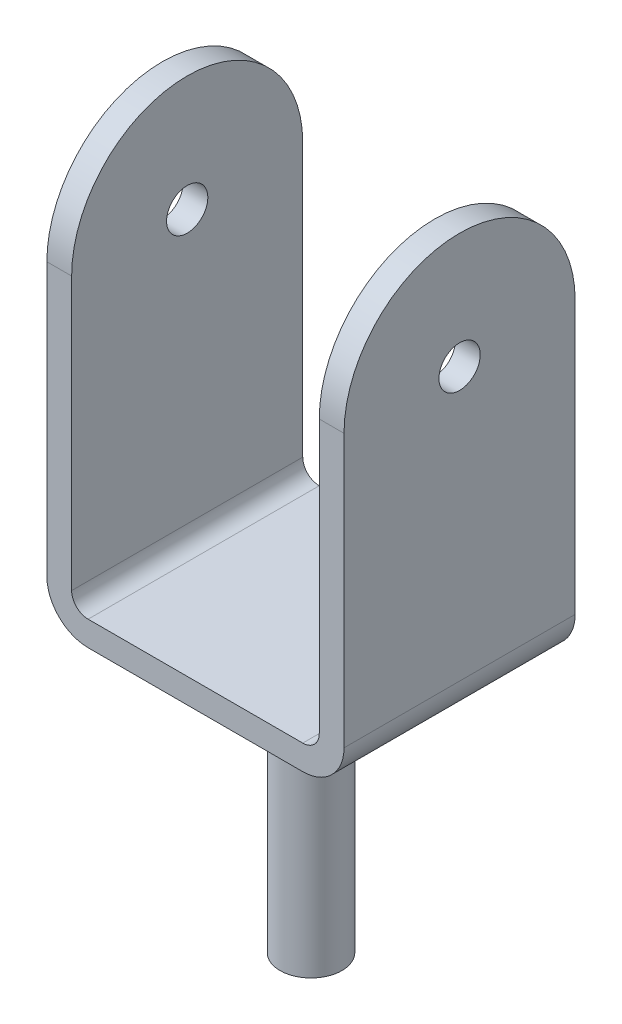
SolidWorks part; units mm, degrees
ref_plane "Front Plane" through (0, 0, 0) normal (0, 0, 1) x (1, 0, 0)
ref_plane "Top Plane" through (0, 0, 0) normal (0, 1, 0) x (1, 0, 0)
ref_plane "Right Plane" through (0, 0, 0) normal (1, 0, 0) x (0, 0, -1)
sketch "Sketch1" plane through (0, 0, 0) normal (0, 1, 0) x (1, 0, 0)
  circle A0 centre (0, 0) radius 37.5
  dimension "D1" = 75
extrude "Boss-Extrude1" add sketch "Sketch1" along normal blind 325 contours A0
sketch "Sketch2" plane through (0, 325, 0) normal (0, 1, 0) x (1, 0, 0)
  line L1 (-180, -140) -> (180, -140)
  line L2 (-180, -140) -> (-180, 140)
  line L3 (-180, 140) -> (180, 140)
  line L4 (180, -140) -> (180, 140)
  line L5 (0, 140) -> (0, -140) construction
  line L6 (-180, 0) -> (180, 0) construction
  point P0 (0, 0)
  dimension "D1" = 280
  dimension "D2" = 360
extrude "Boss-Extrude2" add sketch "Sketch2" along normal blind 520
sketch "Sketch3" plane through (0, 0, 140) normal (0, 0, 1) x (1, 0, 0)
  line L0 (-150, 845) -> (150, 845)
  line L1 (-180, 845) -> (180, 845) construction
  line L2 (-150, 845) -> (-150, 355)
  line L6 (-150, 355) -> (150, 355)
  line L7 (-180, 325) -> (180, 325) construction
  line L8 (-180, 325) -> (180, 325)
  line L9 (150, 845) -> (150, 355)
  line M5 (180, 845) -> (-180, 845)
  dimension "D2" = 30
  dimension "D3" = 30
extrude "Cut-Extrude1" cut sketch "Sketch3" against normal blind 367 contours L9 L2 L6 M5
fillet "Fillet1" radius 20 2 edges at (150, 355, 0) (-150, 355, 0)
fillet "Fillet3" radius 50 2 edges at (180, 325, 0) (-180, 325, 0)
sketch "Sketch4" plane through (180, 0, 0) normal (1, 0, 0) x (0, 0, -1)
  line L0 (-140, 705) -> (-140, 845)
  line L2 (-140, 845) -> (140, 845)
  line L3 (140, 845) -> (140, 705)
  circle A0 centre (0, 705) radius 140
  circle A1 centre (0, 705) radius 25
  line M1 (-140, 845) -> (-140, 375)
  line M5 (140, 375) -> (140, 845)
  line M6 (140, 845) -> (-140, 845)
  dimension "D1" = 280
  dimension "D2" = 50
extrude "Cut-Extrude2" cut sketch "Sketch4" against normal blind 367 contours A0 L2 M1 | A0 M5 M6 | A1
